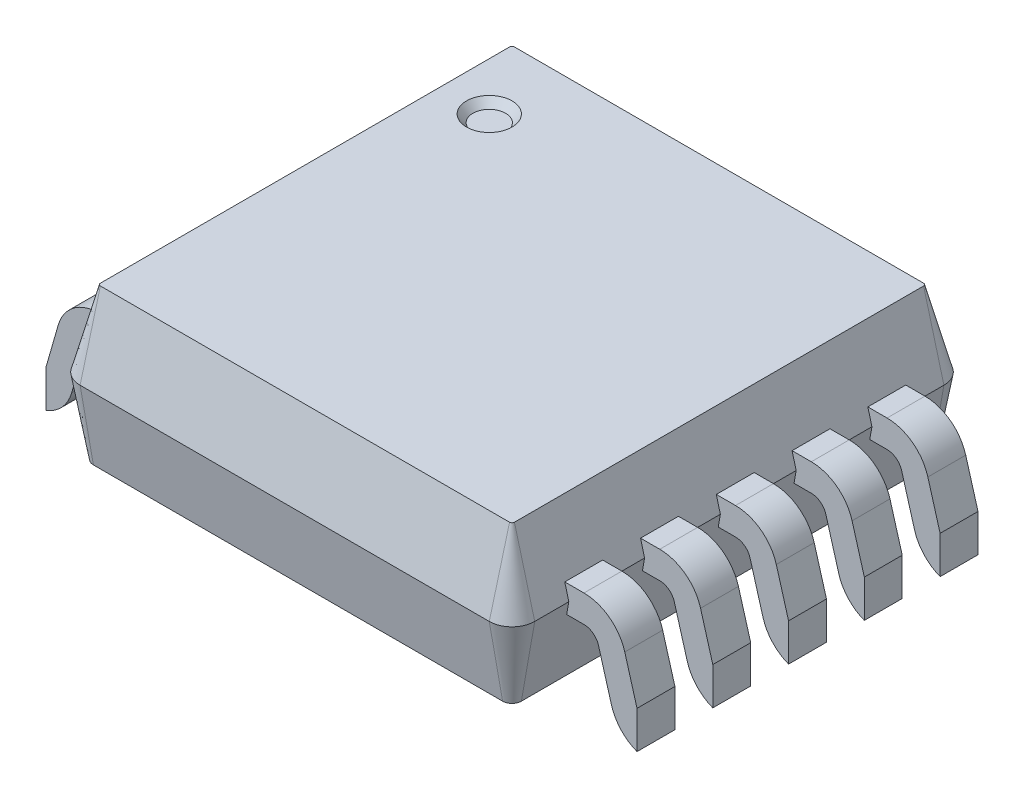
SolidWorks part; units mm, degrees
other "Camera1"
ref_plane "Front" through (0, 0, 0) normal (0, 0, 1) x (1, 0, 0)
ref_plane "Top" through (0, 0, 0) normal (0, 1, 0) x (1, 0, 0)
ref_plane "Right" through (0, 0, 0) normal (1, 0, 0) x (0, 0, -1)
sketch "Sketch1" plane through (0, 0, 0) normal (0, 1, 0) x (1, 0, 0)
  line L0 (-1.35, 1.35) -> (1.35, -1.35) construction
  line L1 (-1.35, 1.5) -> (1.35, 1.5)
  line L2 (-1.5, 1.35) -> (-1.5, -1.35)
  line L3 (-1.35, -1.5) -> (1.35, -1.5)
  line L4 (1.5, 1.35) -> (1.5, -1.35)
  arc A0 (-1.5, 1.35) -> (-1.35, 1.5) centre (-1.35, 1.35) cw
  arc A1 (1.5, 1.35) -> (1.35, 1.5) centre (1.35, 1.35) ccw
  arc A2 (1.35, -1.5) -> (1.5, -1.35) centre (1.35, -1.35) ccw
  arc A3 (-1.5, -1.35) -> (-1.35, -1.5) centre (-1.35, -1.35) ccw
  point P0 (0, 0)
  dimension "D1" = 0.15
  dimension "D2" = 0.15
  dimension "D3" = 0.15
  dimension "D4" = 0.15
  dimension "D5" = 3
  dimension "D6" = 3
extrude "Extrude1" add sketch "Sketch1" along normal blind 0.5 draft 15 and the other way blind 0.5 draft 10 from offset 0.65
sketch "Sketch2" plane through (0, 1.15, 0) normal (0, 1, 0) x (1, 0, 0)
  circle A0 centre (-1.05, 0.9) radius 0.15
sketch "Sketch3" plane through (0, 0, 0) normal (0, 0, 1) x (1, 0, 0)
  line L0 (-2.45, 0) -> (-2.05, 0)
  line L1 (1.45, 0.75) -> (1.6, 0.75)
  line L2 (1.45, 0.57) -> (1.45, 0.75)
  line L3 (2.45, 0.18) -> (2.05, 0.18)
  line L4 (2.45, 0) -> (2.45, 0.18)
  line L5 (1.45, 0.57) -> (1.6, 0.57)
  line L6 (0, 0.15) -> (0, 1.15) construction
  line L7 (1.6961, 0.4976) -> (1.7809, 0.2026)
  line L8 (-1.35, 0.15) -> (1.35, 0.15) construction
  line L9 (1.8691, 0.5474) -> (1.9539, 0.2524)
  line L10 (-1.35, 1.15) -> (1.35, 1.15) construction
  line L11 (2.45, 0) -> (2.05, 0)
  line L27 (-1.8691, 0.5474) -> (-1.9539, 0.2524)
  line L28 (-1.6961, 0.4976) -> (-1.7809, 0.2026)
  line L29 (-1.45, 0.57) -> (-1.6, 0.57)
  line L30 (-2.45, 0) -> (-2.45, 0.18)
  line L31 (-2.45, 0.18) -> (-2.05, 0.18)
  line L32 (-1.45, 0.57) -> (-1.45, 0.75)
  line L33 (-1.45, 0.75) -> (-1.6, 0.75)
  arc A0 (1.9539, 0.2524) -> (2.05, 0.18) centre (2.05, 0.28) ccw
  arc A1 (1.6961, 0.4976) -> (1.6, 0.57) centre (1.6, 0.47) ccw
  arc A2 (1.7809, 0.2026) -> (2.05, 0) centre (2.05, 0.28) ccw
  arc A3 (1.8691, 0.5474) -> (1.6, 0.75) centre (1.6, 0.47) ccw
  arc A12 (-1.8691, 0.5474) -> (-1.6, 0.75) centre (-1.6, 0.47) cw
  arc A13 (-1.7809, 0.2026) -> (-2.05, 0) centre (-2.05, 0.28) cw
  arc A14 (-1.6961, 0.4976) -> (-1.6, 0.57) centre (-1.6, 0.47) cw
  arc A15 (-1.9539, 0.2524) -> (-2.05, 0.18) centre (-2.05, 0.28) cw
  dimension "D1" = 0.45
  dimension "D2" = 0.75
  dimension "D3" = 0.18
  dimension "D4" = 0.28
  dimension "D5" = 0.4
  dimension "D6" = 1
  dimension "D7" = 2.45
extrude "ICE1" add sketch "Sketch3" along normal blind 0.125 and the other way blind 0.125 from offset 1
pattern_linear "LPattern1" count 5 spacing 0.5 along (0, 0, -1) of "ICE1"
extrude "ICE2" cut sketch "Sketch2" against normal blind 0.05 draft 40
sketch "Sketch4" plane through (2.45, 0, 0) normal (1, 0, 0) x (0, 0, -1)
  line L1 (-5.7019, 0.6634) -> (3.6618, 0.6634)
  line L2 (-5.7019, 0.6634) -> (-5.7019, -0.4737)
  line L3 (-5.7019, -0.4737) -> (3.6618, -0.4737)
  line L4 (3.6618, 0.6634) -> (3.6618, -0.4737)
  line L5 (-5.7019, 0.6634) -> (3.6618, -0.4737) construction
  line L6 (-5.7019, -0.4737) -> (3.6618, 0.6634) construction
  point P0 (-1.0201, 0.0948)
extrude "Cut-Extrude1" cut sketch "Sketch4" against normal blind 0.5 contours L1 L4 L3 L2
sketch "Sketch5" plane through (-2.45, 0, 0) normal (-1, 0, 0) x (0, 0, 1)
  line L1 (-2.0263, -0.2617) -> (3.9757, -0.2617)
  line L2 (-2.0263, -0.2617) -> (-2.0263, 0.4047)
  line L3 (-2.0263, 0.4047) -> (3.9757, 0.4047)
  line L4 (3.9757, -0.2617) -> (3.9757, 0.4047)
  line L5 (-2.0263, -0.2617) -> (3.9757, 0.4047) construction
  line L6 (-2.0263, 0.4047) -> (3.9757, -0.2617) construction
  point P0 (0.9747, 0.0715)
extrude "Cut-Extrude2" cut sketch "Sketch5" against normal blind 0.5
